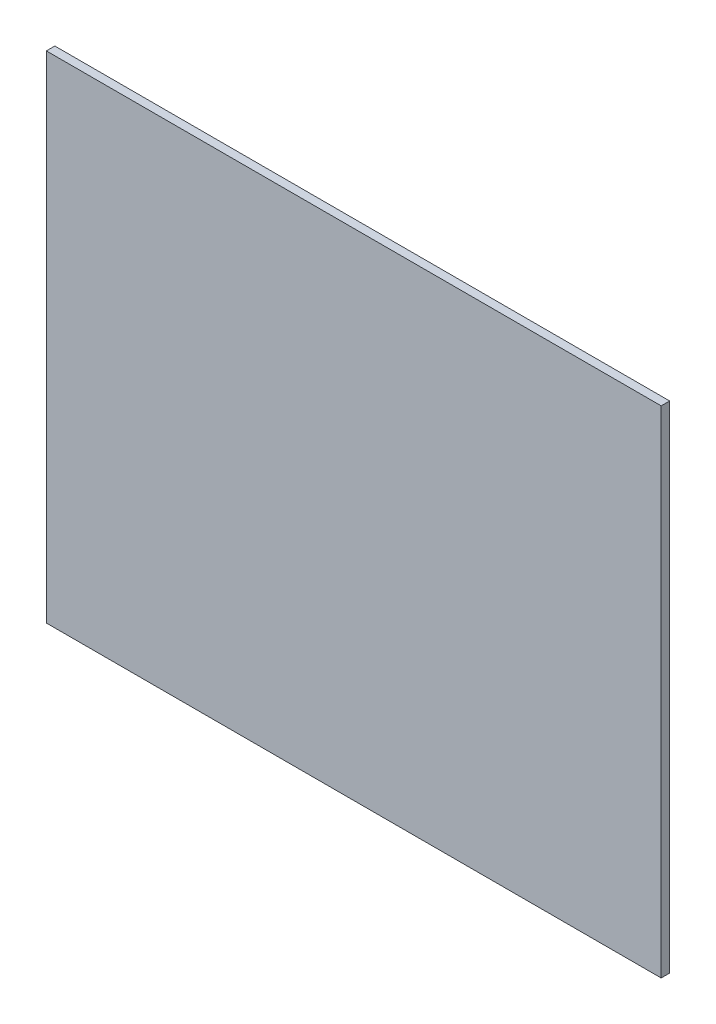
SolidWorks part; units mm, degrees
ref_plane "Front Plane" through (0, 0, 0) normal (0, 0, 1) x (1, 0, 0)
ref_plane "Top Plane" through (0, 0, 0) normal (0, 1, 0) x (1, 0, 0)
ref_plane "Right Plane" through (0, 0, 0) normal (1, 0, 0) x (0, 0, -1)
sketch "Sketch1" plane through (0, 0, 0) normal (0, 0, 1) x (1, 0, 0)
  line L1 (-157.5816, -127) -> (157.5816, -127)
  line L2 (-157.5816, -127) -> (-157.5816, 127)
  line L3 (-157.5816, 127) -> (157.5816, 127)
  line L4 (157.5816, -127) -> (157.5816, 127)
  line L5 (-157.5816, -127) -> (157.5816, 127) construction
  line L6 (-157.5816, 127) -> (157.5816, -127) construction
  point P0 (0, 0)
  dimension "D1" = 315.1632
  dimension "D2" = 254
extrude "Boss-Extrude1" add sketch "Sketch1" along normal blind 4.3434
